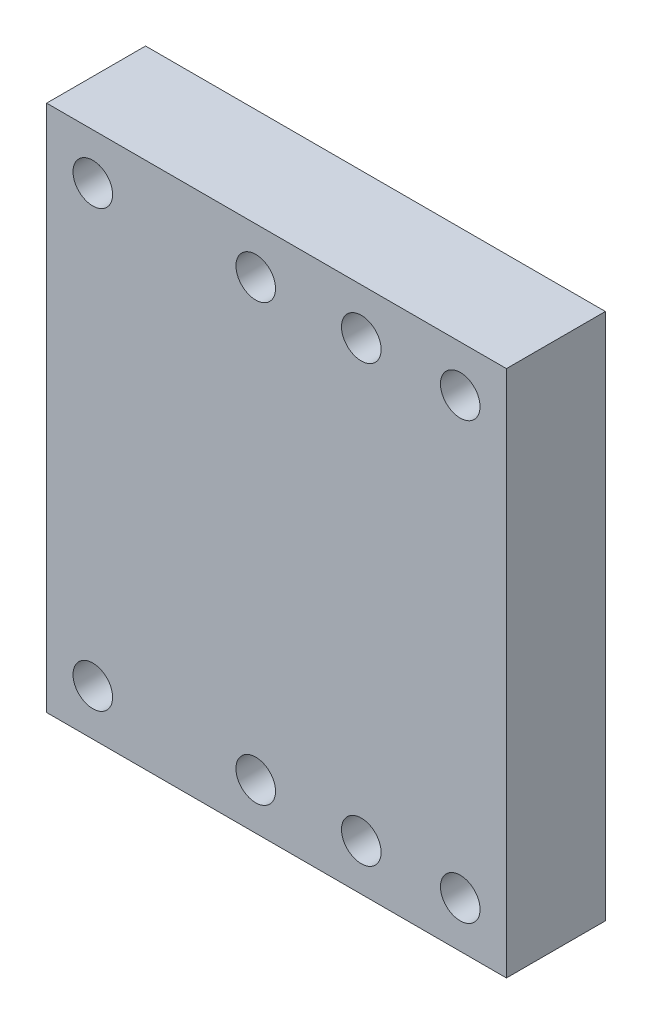
SolidWorks part; units mm, degrees
ref_plane "Płaszczyzna przednia" through (0, 0, 0) normal (0, 0, 1) x (1, 0, 0)
ref_plane "Płaszczyzna górna" through (0, 0, 0) normal (0, 1, 0) x (1, 0, 0)
ref_plane "Płaszczyzna prawa" through (0, 0, 0) normal (1, 0, 0) x (0, 0, -1)
sketch "Szkic1" plane through (0, 0, 0) normal (0, 0, 1) x (1, 0, 0)
  line L6 (-34.85, -40) -> (34.85, -40)
  line L11 (34.85, -40) -> (34.85, 40)
  line L12 (34.85, 40) -> (-34.85, 40)
  line L13 (-34.85, 40) -> (-34.85, -40)
  line L15 (34.85, 40) -> (-34.85, -40) construction
  line L16 (-34.85, 40) -> (34.85, -40) construction
  point P0 (0, 0)
  point P1 (0, 0)
  dimension "D2" = 80
  dimension "D4" = 69.7
extrude "Dodanie-wyciągnięcie1" add sketch "Szkic1" along normal blind 15
sketch "Szkic3" plane through (0, 0, 0) normal (0, 0, -1) x (1, 0, 0)
  line L0 (-34.85, 40) -> (34.85, 40) construction
  line L3 (34.85, -40) -> (-34.85, -40) construction
  line L5 (34.85, 40) -> (34.85, -40) construction
  circle A0 centre (12.85, 33) radius 3
  circle A1 centre (-3.15, 33) radius 3
  circle A2 centre (-3.15, -33) radius 3
  circle A3 centre (12.85, -33) radius 3
  dimension "D1" = 7
  dimension "D5" = 6
  dimension "D2" = 22
  dimension "D4" = 7
  dimension "D7" = 16
extrude "Wytnij-wyciągnięcie1" cut sketch "Szkic3" against normal blind 15
sketch "Szkic4" plane through (0, 0, 0) normal (0, 0, 1) x (-1, 0, 0)
  circle A0 centre (3.15, 33) radius 5
  circle A1 centre (-12.85, 33) radius 5
  circle A2 centre (-12.85, -33) radius 5
  circle A3 centre (3.15, -33) radius 5
  dimension "D1" = 10
extrude "Wytnij-wyciągnięcie2" cut sketch "Szkic4" along normal blind 7
sketch "Szkic5" plane through (0, 0, 15) normal (0, 0, 1) x (1, 0, 0)
  line L0 (34.85, 40) -> (-34.85, 40) construction
  line L1 (-34.85, 40) -> (-34.85, -40) construction
  line L2 (34.85, -40) -> (34.85, 40) construction
  line L4 (-34.85, -40) -> (34.85, -40) construction
  circle A0 centre (-27.85, 33) radius 3
  circle A1 centre (27.85, 33) radius 3
  circle A2 centre (27.85, -33) radius 3
  circle A3 centre (-27.85, -33) radius 3
  dimension "D1" = 7
  dimension "D5" = 6
  dimension "D6" = 6
  dimension "D7" = 6
  dimension "D8" = 6
  dimension "D2" = 7
  dimension "D3" = 7
  dimension "D4" = 7
extrude "Wytnij-wyciągnięcie3" cut sketch "Szkic5" against normal blind 15
